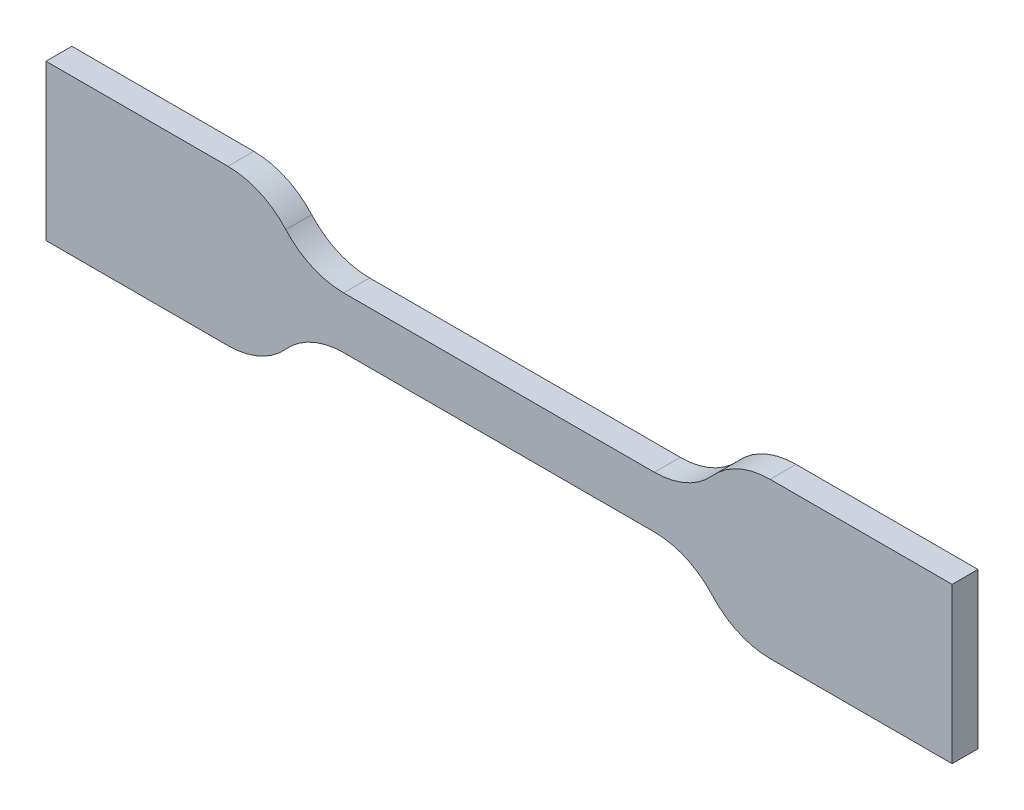
SolidWorks part; units mm, degrees
other "ISO_527-2_type_5B"
ref_plane "Front Plane" through (0, 0, 0) normal (0, 0, 1) x (1, 0, 0)
ref_plane "Top Plane" through (0, 0, 0) normal (0, 1, 0) x (1, 0, 0)
ref_plane "Right Plane" through (0, 0, 0) normal (1, 0, 0) x (0, 0, -1)
other "Configuration Table"
sketch "Sketch1" plane through (0, 0, 0) normal (0, 0, 1) x (1, 0, 0)
  line L0 (-17.5, 3) -> (-17.5, -3)
  line L1 (-17.5, -3) -> (-10.4721, -3)
  line L2 (-17.5, 3) -> (-10.4721, 3)
  line L3 (10.4721, 3) -> (17.5, 3)
  line L4 (17.5, 3) -> (17.5, -3)
  line L5 (17.5, -3) -> (10.4721, -3)
  line L6 (-6, 1) -> (6, 1)
  line L7 (-6, -1) -> (6, -1)
  arc A0 (-10.4721, 3) -> (-8.2361, 2) centre (-10.4721, 0) cw
  arc A1 (-8.2361, 2) -> (-6, 1) centre (-6, 4) ccw
  arc A2 (-6, -1) -> (-8.2361, -2) centre (-6, -4) ccw
  arc A3 (-8.2361, -2) -> (-10.4721, -3) centre (-10.4721, 0) cw
  arc A4 (6, 1) -> (8.2361, 2) centre (6, 4) ccw
  arc A5 (8.2361, 2) -> (10.4721, 3) centre (10.4721, 0) cw
  arc A6 (10.4721, -3) -> (8.2361, -2) centre (10.4721, 0) cw
  arc A7 (8.2361, -2) -> (6, -1) centre (6, -4) ccw
  point P7 (-17.5, 0)
  point P26 (0, 1)
  dimension "small_radius" = 3
  dimension "large_radius" = 3
  dimension "width_at_ends" = 6
  dimension "overall_length" = 35
  dimension "length_narrow_sided_portion" = 12
  dimension "width_narrow_portion" = 2
extrude "Boss-Extrude1" add sketch "Sketch1" along normal mid plane 1
